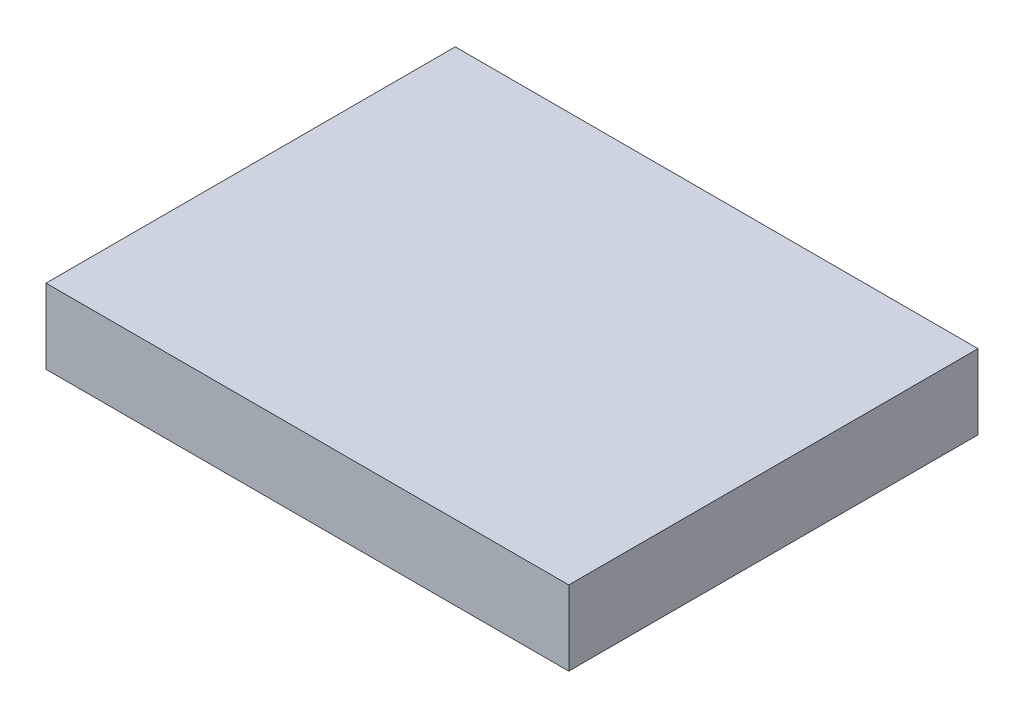
SolidWorks part; units mm, degrees
ref_plane "Front Plane" through (0, 0, 0) normal (0, 0, 1) x (1, 0, 0)
ref_plane "Top Plane" through (0, 0, 0) normal (0, 1, 0) x (1, 0, 0)
ref_plane "Right Plane" through (0, 0, 0) normal (1, 0, 0) x (0, 0, -1)
sketch "Sketch1" plane through (0, 0, 0) normal (0, 1, 0) x (1, 0, 0)
  line L1 (-22.225, -17.399) -> (22.225, -17.399)
  line L2 (-22.225, -17.399) -> (-22.225, 17.399)
  line L3 (-22.225, 17.399) -> (22.225, 17.399)
  line L4 (22.225, -17.399) -> (22.225, 17.399)
  line L5 (-22.225, -17.399) -> (22.225, 17.399) construction
  line L6 (-22.225, 17.399) -> (22.225, -17.399) construction
  point P0 (0, 0)
  dimension "D1" = 44.45
  dimension "D2" = 34.798
extrude "Boss-Extrude1" add sketch "Sketch1" along normal mid plane 6.35
